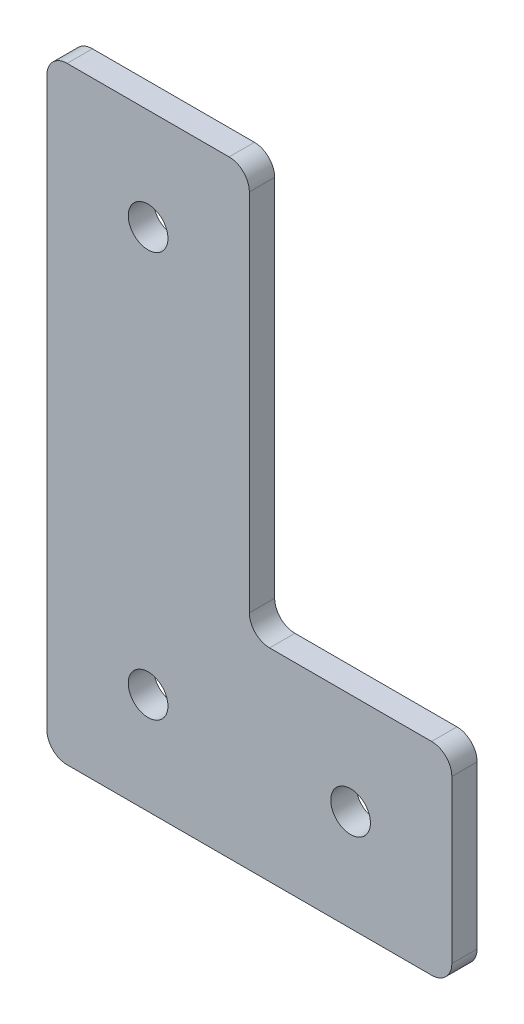
SolidWorks part; units mm, degrees
ref_plane "Front Plane" through (0, 0, 0) normal (0, 0, 1) x (1, 0, 0)
ref_plane "Top Plane" through (0, 0, 0) normal (0, 1, 0) x (1, 0, 0)
ref_plane "Right Plane" through (0, 0, 0) normal (1, 0, 0) x (0, 0, -1)
sketch "Sketch1" plane through (0, 0, 0) normal (0, 0, 1) x (1, 0, 0)
  line L0 (0, 73.66) -> (0, 2.54)
  line L1 (2.54, 0) -> (48.26, 0)
  line L2 (50.8, 2.54) -> (50.8, 22.86)
  line L3 (48.26, 25.4) -> (27.94, 25.4)
  line L4 (25.4, 27.94) -> (25.4, 73.66)
  line L5 (22.86, 76.2) -> (2.54, 76.2)
  arc A0 (48.26, 0) -> (50.8, 2.54) centre (48.26, 2.54) ccw
  arc A1 (50.8, 22.86) -> (48.26, 25.4) centre (48.26, 22.86) ccw
  arc A2 (27.94, 25.4) -> (25.4, 27.94) centre (27.94, 27.94) cw
  arc A3 (0, 2.54) -> (2.54, 0) centre (2.54, 2.54) ccw
  arc A4 (25.4, 73.66) -> (22.86, 76.2) centre (22.86, 73.66) ccw
  arc A5 (0, 73.66) -> (2.54, 76.2) centre (2.54, 73.66) cw
  circle A6 centre (12.7, 63.5) radius 2.4892
  circle A8 centre (12.7, 12.7) radius 2.4892
  circle A9 centre (38.1, 12.7) radius 2.4892
  point P4 (0, 38.1)
  point P10 (50.8, 0)
  point P17 (0, 0)
  point P22 (0, 76.2)
  point P31 (0, 0)
  point P32 (0, 0)
  point P33 (50.8, 12.7)
  point P34 (0, 0)
  point P35 (0, 0)
  point P36 (12.7, 76.2)
  point P37 (0, 0)
  dimension "D5" = 2.54
  dimension "D6" = 4.9784
  dimension "D7" = 25.4
  dimension "D8" = 50.8
  dimension "D10" = 12.7
  dimension "D1" = 50.8
  dimension "D2" = 76.2
  dimension "D3" = 25.4
  dimension "D4" = 25.4
extrude "Boss-Extrude1" add sketch "Sketch1" along normal blind 3.175
